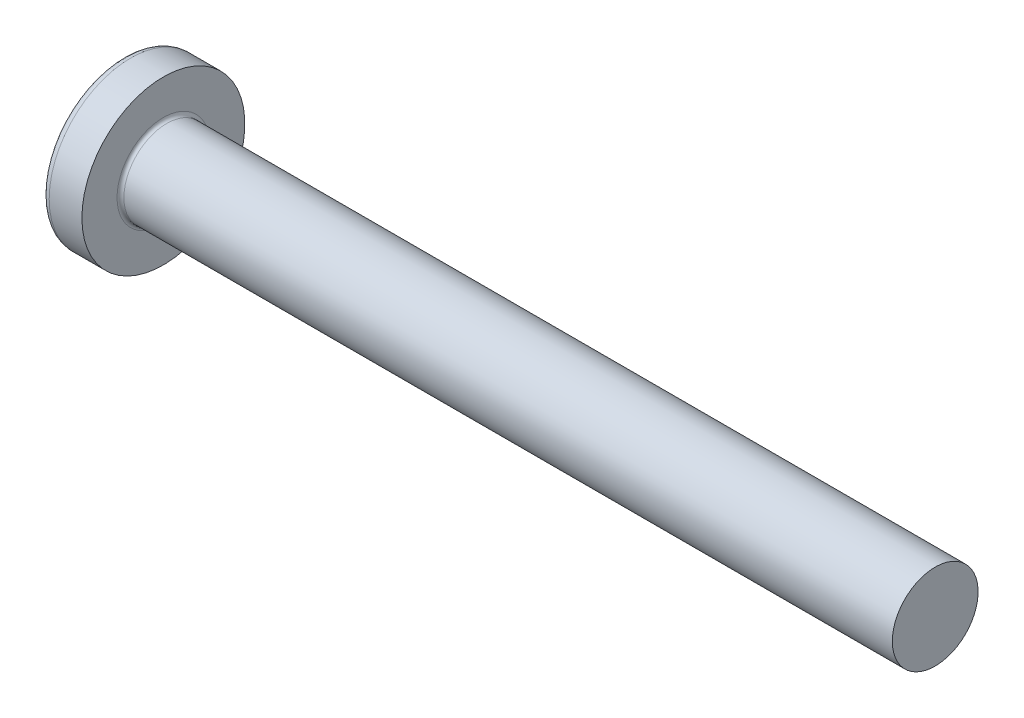
SolidWorks part; units mm, degrees
ref_plane "Plane1" through (0, 0, 0) normal (0, 0, 1) x (1, 0, 0)
ref_plane "Plane2" through (0, 0, 0) normal (0, 1, 0) x (1, 0, 0)
ref_plane "Plane3" through (0, 0, 0) normal (1, 0, 0) x (0, 0, -1)
sketch "BodySke" plane through (0, 0, 0) normal (0, 0, 1) x (1, 0, 0)
  line L0 (3.7, 2.5) -> (3.7, 4.75)
  line L1 (4.1, 6.35) -> (4.1, -3.175) construction
  line L2 (-25.4, 0) -> (127, 0) construction
  line L3 (48.7, 0) -> (0, 0)
  line L4 (3.7, 2.5) -> (48.7, 2.5)
  line L5 (48.7, 2.5) -> (48.7, 0)
  line L6 (1.7942, 4.75) -> (3.7, 4.75)
  line L8 (3.7, 6.35) -> (3.7, -3.175) construction
  arc A0 (1.4243, 4.5563) -> (0, 0) centre (8, 0) ccw
  arc A2 (1.4243, 4.5563) -> (1.7942, 4.75) centre (1.7942, 4.3) cw
  dimension "Head_fillet_rad" = 0.45
  dimension "Head_crown_rad" = 8
  dimension "Head_ht" = 3.7
  dimension "Diameter" = 5
  dimension "Length" = 45
  dimension "Head_dia" = 9.5
  dimension "Advance" = 0.8
  dimension "Thread_nom" = 45
revolve "Base-Revolve" add sketch "BodySke"
cosmetic thread "ThreadCosmetic"
fillet "Fillet1" radius 0.2 1 edges at (3.7, 0, 2.5)
sketch "Sketch3" plane through (0, 0, 0) normal (1, 0, 0) x (0, 0, -1)
  line L0 (0.515, -2.35) -> (-0.515, -2.35)
  line L1 (0.515, -2.35) -> (0.515, 2.35)
  line L2 (-0.515, 2.35) -> (0.515, 2.35)
  line L3 (-0.515, 2.35) -> (-0.515, -2.35)
  dimension "D1" = 2.35
  dimension "Cross_dia" = 4.7
  dimension "D2" = 0.515
  dimension "Cross_width" = 1.03
ref_plane "Plane4" through (2.74, 0, 0) normal (1, 0, 0) x (0, 0, -1)
sketch "Sketch4" plane through (2.74, 0, 0) normal (1, 0, 0) x (0, 0, -1)
  line L0 (0.515, -0.9839) -> (-0.515, -0.9839)
  line L1 (0.515, -0.9839) -> (0.515, 0.9839)
  line L2 (-0.515, 0.9839) -> (0.515, 0.9839)
  line L3 (-0.515, 0.9839) -> (-0.515, -0.9839)
  dimension "D1" = 1.03
  dimension "D2" = 1.9678
  dimension "D3" = 0.515
  dimension "D4" = 0.9839
loft "Recess" cut profiles "Sketch3", "Sketch4"
pattern_circular "RecPat" count 2 every 90 about axis through (0, 0, 0) along (1, 0, 0) of "Recess"
sketch "RecCorSke" plane through (0, 0, 0) normal (0, 0, 1) x (1, 0, 0)
  line L0 (-3.175, 0) -> (15.875, 0) construction
  line L1 (-25.4, 0) -> (127, 0) construction
  line L2 (0, 0) -> (0, 1.0426)
  line L3 (0, 1.0426) -> (2.74, 0.851)
  line L4 (2.74, 0.851) -> (3.0165, 0)
  line L5 (3.0165, 0) -> (0, 0)
  dimension "Diameter" = 1.702
  dimension "Depth" = 2.74
  dimension "Draft_angle" = 4
  dimension "Bottom_angle" = 18
revolve "RecessCore" cut sketch "RecCorSke" angle 360 about L0
sketch "ThdSchSke" plane through (0, 0, 0) normal (0, 0, 1) x (1, 0, 0)
  line L0 (5.3, -2.055) -> (4.9884, -2.5)
  line L1 (5.3, -2.055) -> (5.6116, -2.5)
  line L2 (5.6116, -2.5) -> (5.6116, -3.125)
  line L3 (-3.175, 0) -> (5.1513, 0) construction
  line L5 (5.6116, -3.125) -> (4.9884, -3.125)
  line L6 (4.9884, -3.125) -> (4.9884, -2.5)
  dimension "Thread_minor" = 4.11
  dimension "Diameter" = 5
  dimension "Start" = 5.3
  dimension "SideAngle" = 55
  dimension "VeeAngle" = 70
  dimension "Overcut" = 6.25
revolve "ThreadSchematic" [suppressed] cut sketch "ThdSchSke" angle 360 about L3
pattern_linear "ThdSchPat" [suppressed]
equation "\"D1@Sketch3\" = \"Cross_dia@Sketch3\" / 2"
equation "\"D2@Sketch3\" = \"Cross_width@Sketch3\" / 2"
equation "\"Depth@RecCorSke\" = \"Cross_depth@Plane4\""
equation "\"D1@Sketch4\" = \"Cross_width@Sketch3\""
equation "\"D2@Sketch4\" = \"Cross_dia@Sketch3\" - 2.0 * \"Cross_depth@Plane4\" * tan(26.5  * 0.017453292)"
equation "\"D3@Sketch4\" = \"D1@Sketch4\" / 2"
equation "\"D4@Sketch4\" = \"D2@Sketch4\" / 2"
equation "\"Thread_length@ThreadCosmetic\" = ((sgn( (\"Length@BodySke\" - \"Advance@BodySke\" * 2.0 ) - \"Thread_nom@BodySke\" )-1)*( (\"Length@BodySke\" - \"Advance@BodySke\" * 2.0 ) - \"Thread_nom@BodySke\" ))/-2+ \"Thread_nom@BodySke\""
equation "\"Thread_minor@ThdSchSke\" = \"Thread_minor@ThreadCosmetic\""
equation "\"Diameter@ThdSchSke\" = \"Diameter@BodySke\""
equation "\"Overcut@ThdSchSke\" = \"Diameter@BodySke\" * 1.25"
equation "\"Start@ThdSchSke\" = \"Head_ht@BodySke\" + \"Length@BodySke\" - \"Thread_length@ThreadCosmetic\"  '---Non-countersunk---"
equation "\"Num_threads@ThdSchPat\" = int( \"Thread_length@ThreadCosmetic\" / \"Advance@BodySke\" + 0.999 )  + 1"
equation "\"Advance@ThdSchPat\" = \"Thread_length@ThreadCosmetic\" /  (\"Num_threads@ThdSchPat\" - 1) 'relax it"
